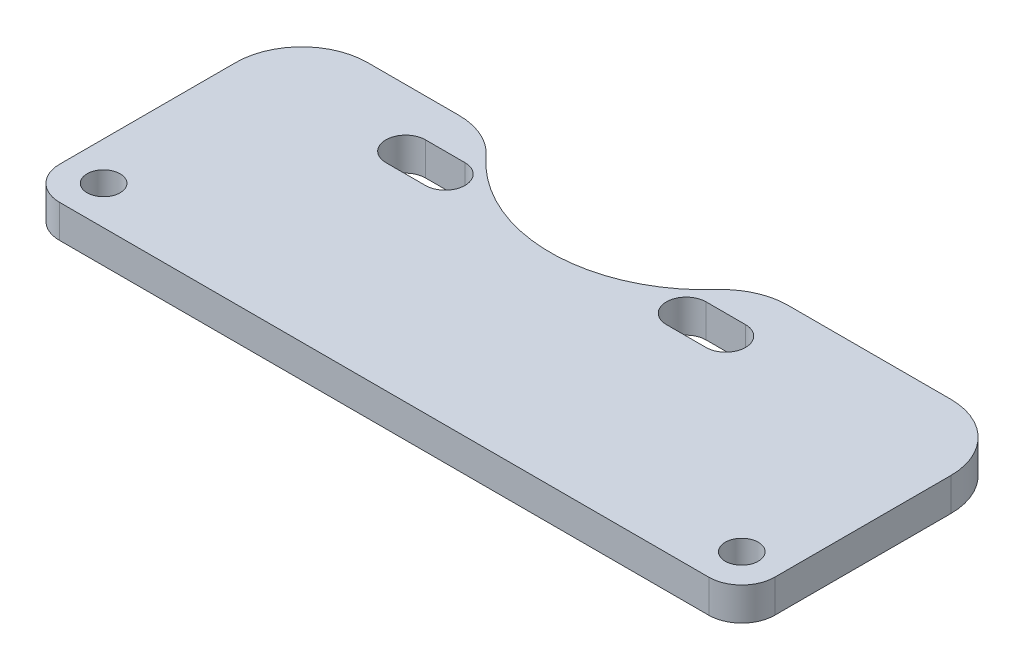
SolidWorks part; units mm, degrees
ref_plane "前视基准面" through (0, 0, 0) normal (0, 0, 1) x (1, 0, 0)
ref_plane "上视基准面" through (0, 0, 0) normal (0, 1, 0) x (1, 0, 0)
ref_plane "右视基准面" through (0, 0, 0) normal (1, 0, 0) x (0, 0, -1)
sketch "Sketch1" plane through (0, 0, 0) normal (0, 1, 0) x (1, 0, 0)
  line L0 (-42.5, -28) -> (22.5, -28)
  line L1 (-42.5, -28) -> (-42.5, -3)
  line L2 (22.5, -28) -> (22.5, -3)
  line L3 (-42.5, -3) -> (22.5, -3)
  line L4 (-42.5, -28) -> (42.5, -28) construction
  line L5 (-42.5, -28) -> (-42.5, 28) construction
  line L6 (42.5, -28) -> (42.5, 28) construction
  line L7 (-42.5, 28) -> (42.5, 28) construction
  line L8 (-42.5, 0) -> (42.5, 0) construction
  line L9 (-24.2027, -8.25) -> (-27.7973, -8.25) construction
  line L10 (-28.25, 19.5) -> (1.75, 19.5) construction
  line L11 (-28.25, 19.5) -> (-28.25, -10.5) construction
  line L12 (-28.25, -10.5) -> (1.75, -10.5) construction
  line L13 (1.75, 19.5) -> (1.75, -10.5) construction
  line L14 (-28.25, 19.5) -> (1.75, -10.5) construction
  line L15 (-28.25, -10.5) -> (1.75, 19.5) construction
  line L18 (-24.2027, -10.0473) -> (-27.7973, -10.0473)
  line L19 (-24.2027, -6.4527) -> (-27.7973, -6.4527)
  line L20 (-2.2973, -8.25) -> (1.2973, -8.25) construction
  line L21 (-2.2973, -6.4527) -> (1.2973, -6.4527)
  line L22 (-2.2973, -10.0473) -> (1.2973, -10.0473)
  circle A0 centre (-39, -24.5) radius 1.5
  circle A1 centre (19, -24.5) radius 1.5
  circle A2 centre (-13.25, 4.5) radius 14.15
  circle A3 centre (-26, -8.25) radius 1.7973 construction
  circle A4 centre (-0.5, -8.25) radius 1.7973 construction
  arc A7 (-24.2027, -10.0473) -> (-24.2027, -6.4527) centre (-24.2027, -8.25) ccw
  arc A8 (-27.7973, -6.4527) -> (-27.7973, -10.0473) centre (-27.7973, -8.25) ccw
  arc A9 (-2.2973, -6.4527) -> (-2.2973, -10.0473) centre (-2.2973, -8.25) ccw
  arc A10 (1.2973, -10.0473) -> (1.2973, -6.4527) centre (1.2973, -8.25) ccw
  point P26 (-26, -8.25)
  point P33 (-0.5, -8.25)
  dimension "D1" = 3
  dimension "D2" = 58
  dimension "D3" = 3.5
  dimension "D4" = 3.5
  dimension "D5" = 3.5
  dimension "D8" = 25.75
  dimension "D9" = 32.5
  dimension "D10" = 28.3
  dimension "D12" = 4.5
  dimension "D6" = 56
  dimension "D7" = 85
  dimension "D11" = 30
  dimension "D13" = 25
extrude "Boss-Extrude1" add sketch "Sketch1" along normal blind 3 contours A2 L3 L1 L0 L2 A10 L22 A9 L21 A8 L19 A7 L18 A1 A0
fillet "Fillet1" radius 3 2 edges at (22.5, 1.5, 28) (-42.5, 1.5, 28)
fillet "Fillet2" radius 6 4 edges at (-25.2489, 1.5, 3) (-1.2511, 1.5, 3) (22.5, 1.5, 3) (-42.5, 1.5, 3)
